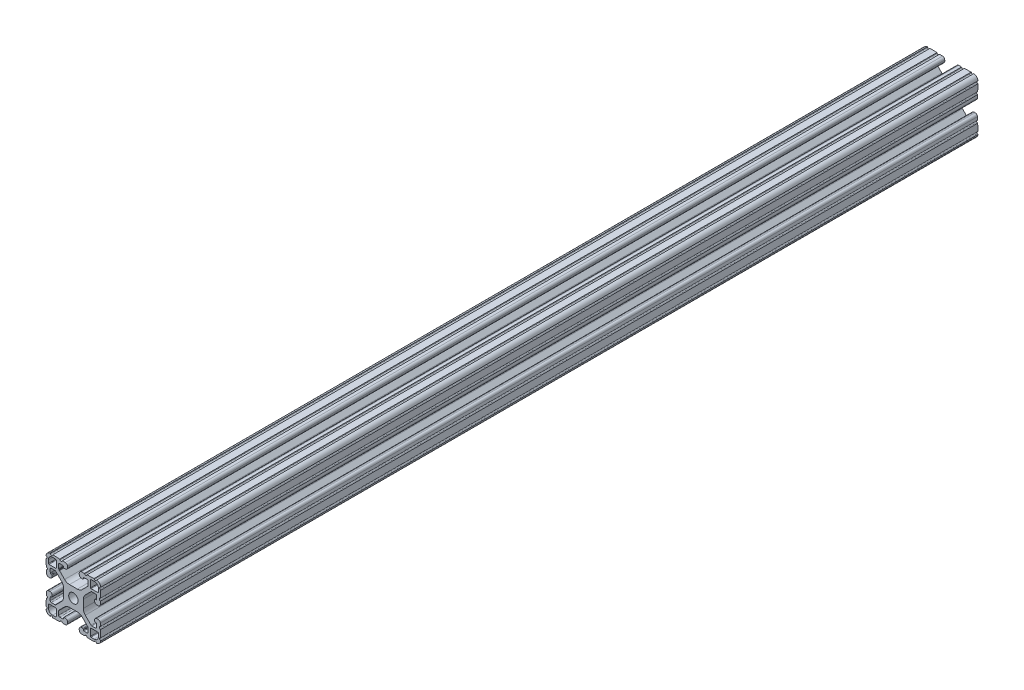
SolidWorks part; units mm, degrees
ref_plane "Front Plane" through (0, 0, 0) normal (0, 0, 1) x (1, 0, 0)
ref_plane "Top Plane" through (0, 0, 0) normal (0, 1, 0) x (1, 0, 0)
ref_plane "Right Plane" through (0, 0, 0) normal (1, 0, 0) x (0, 0, -1)
sketch "Sketch2" plane through (0, 0, 0) normal (0, 0, 1) x (1, 0, 0)
  line L0 (0, 19.05) -> (0, -19.05) construction
  line L1 (-19.05, 0) -> (19.05, 0) construction
  line L2 (4.064, -19.05) -> (19.05, -19.05) construction
  line L3 (19.05, -19.05) -> (19.05, -4.064) construction
  line L4 (4.064, -19.05) -> (4.064, -15.8768) construction
  line L5 (4.064, -15.8768) -> (13.7215, -15.8768) construction
  line L6 (13.7215, -15.8768) -> (4.7027, -6.858) construction
  line L7 (0, 0) -> (19.05, -19.05) construction
  line L8 (19.05, -4.064) -> (15.8768, -4.064) construction
  line L9 (15.8768, -4.064) -> (15.8768, -13.7215) construction
  line L10 (15.8768, -13.7215) -> (6.858, -4.7027) construction
  line L11 (11.3674, -9.2121) -> (9.2121, -11.3674) construction
  line L12 (10.287, -12.4423) -> (10.287, -15.8768) construction
  line L13 (15.7642, -19.0481) -> (4.064, -18.6395) construction
  line L14 (4.064, -18.6395) -> (4.2014, -14.7049) construction
  line L15 (4.2014, -14.7049) -> (6.858, -14.7977) construction
  line L16 (6.858, -14.7977) -> (6.858, -15.8768) construction
  line L17 (19.05, 4.064) -> (19.05, -4.064) construction
  line L18 (-19.05, -19.05) -> (19.05, -19.05) construction
  line L19 (-19.05, -19.05) -> (-19.05, 19.05) construction
  line L20 (-19.05, 19.05) -> (19.05, 19.05) construction
  line L21 (19.05, -19.05) -> (19.05, 19.05) construction
  line L22 (8.5725, -18.7969) -> (8.6004, -17.9973) construction
  line L23 (15.24, -19.0298) -> (15.2679, -18.2301) construction
  circle A0 centre (0, 0) radius 3.2639 construction
  arc A1 (18.1201, -18.1201) -> (15.7642, -19.0481) centre (15.875, -15.875) cw construction
  point P8 (0, -6.858)
  point P16 (10.2898, -10.2898)
  point P28 (11.8872, -11.8872)
  point P34 (8.5725, -18.7969)
  point P36 (15.24, -19.0298)
  point P38 (19.05, 0)
  dimension "D7" = 1.6002
  dimension "Center Hole Diameter" = 6.5278
  dimension "Corner Radius" = 3.175
  dimension "Slot Depth" = 12.192
  dimension "D1" = 3.048
  dimension "D3" = 2
  dimension "Flange Thickness" = 3.937
  dimension "D4" = 3.1732
  dimension "D2" = 20.574
  dimension "D5" = 13.716
  dimension "D6" = 7.1628
  dimension "D8" = 15.24
  dimension "D9" = 8.5725
  dimension "D10" = 0.8001
  dimension "Rail Height" = 38.1
  dimension "Rail Width" = 38.1
  dimension "T Slot Width" = 8.128
sketch "Sketch3" plane through (0, 0, 0) normal (1, 0, 0) x (0, 0, -1)
  line L0 (-304.8, 19.05) -> (304.8, 19.05) construction
  line L1 (-254, 0) -> (254, 0) construction
  dimension "Length" = 609.6
  dimension "D1" = 50.8
sketch "Sketch4" plane through (0, 0, 0) normal (0, 0, 1) x (1, 0, 0)
  line L1 (6.858, -14.7977) -> (6.858, -15.8768) construction
  line L2 (11.8872, -12.2682) -> (11.8872, -16.9436)
  line L3 (12.2549, -17.3243) -> (14.4454, -17.4008)
  line L7 (12.2682, -11.8872) -> (16.9436, -11.8872)
  line L9 (17.3243, -12.2549) -> (17.4008, -14.4454)
  line L22 (0, 0) -> (19.05, -19.05) construction
  line L23 (15.7642, -19.0481) -> (5.5961, -18.693)
  line L24 (4.064, -17.1065) -> (4.064, -16.344)
  line L25 (5.7069, -14.7575) -> (6.4903, -14.7848)
  line L26 (6.858, -15.1656) -> (6.858, -15.6891)
  line L27 (7.2257, -16.0699) -> (9.4655, -16.1481)
  line L28 (10.287, -15.3549) -> (10.287, -12.771)
  line L29 (10.0545, -12.2098) -> (6.0939, -8.2492)
  line L30 (2.7353, -6.858) -> (0, -6.858)
  line L31 (13.7215, -15.8768) -> (4.7027, -6.858) construction
  line L32 (4.064, -19.05) -> (19.05, -19.05) construction
  line L33 (4.064, -19.05) -> (4.064, -15.8768) construction
  line L34 (0, 19.05) -> (0, -19.05) construction
  line L35 (0, -3.2639) -> (0, -6.858)
  line L36 (0, 0) -> (19.1669, -19.1669) construction
  line L46 (10.287, -12.4423) -> (10.287, -15.8768) construction
  line L47 (6.858, -2.7353) -> (6.858, 0)
  line L48 (12.2098, -10.0545) -> (8.2492, -6.0939)
  line L49 (15.3549, -10.287) -> (12.771, -10.287)
  line L50 (16.0699, -7.2257) -> (16.1481, -9.4655)
  line L51 (15.1656, -6.858) -> (15.6891, -6.858)
  line L52 (14.7575, -5.7069) -> (14.7848, -6.4903)
  line L53 (17.1065, -4.064) -> (16.344, -4.064)
  line L54 (19.0481, -15.7642) -> (18.693, -5.5961)
  line L55 (3.2639, 0) -> (6.858, 0)
  arc A1 (14.4454, -17.4008) -> (17.4008, -14.4454) centre (14.5451, -14.5451) ccw
  arc A10 (16.9436, -11.8872) -> (17.3243, -12.2549) centre (16.9436, -12.2682) cw
  arc A12 (19.0481, -15.7642) -> (15.7642, -19.0481) centre (15.875, -15.875) cw
  arc A13 (3.2639, 0) -> (0, -3.2639) centre (0, 0) cw
  circle A14 centre (0, 0) radius 3.2639 construction
  arc A16 (6.0939, -8.2492) -> (2.7353, -6.858) centre (2.7353, -11.6078) ccw
  arc A17 (5.5961, -18.693) -> (4.064, -17.1065) centre (5.6515, -17.1065) cw
  arc A18 (4.064, -16.344) -> (5.7069, -14.7575) centre (5.6515, -16.344) cw
  arc A19 (9.4655, -16.1481) -> (10.287, -15.3549) centre (9.4933, -15.3549) ccw
  arc A20 (10.287, -12.771) -> (10.0545, -12.2098) centre (9.4933, -12.771) ccw
  arc A21 (6.4903, -14.7848) -> (6.858, -15.1656) centre (6.477, -15.1656) cw
  arc A22 (6.858, -15.6891) -> (7.2257, -16.0699) centre (7.239, -15.6891) ccw
  arc A23 (15.6891, -6.858) -> (16.0699, -7.2257) centre (15.6891, -7.239) cw
  arc A24 (14.7848, -6.4903) -> (15.1656, -6.858) centre (15.1656, -6.477) ccw
  arc A25 (12.771, -10.287) -> (12.2098, -10.0545) centre (12.771, -9.4933) cw
  arc A26 (16.1481, -9.4655) -> (15.3549, -10.287) centre (15.3549, -9.4933) cw
  arc A27 (16.344, -4.064) -> (14.7575, -5.7069) centre (16.344, -5.6515) ccw
  arc A28 (18.693, -5.5961) -> (17.1065, -4.064) centre (17.1065, -5.6515) ccw
  arc A29 (8.2492, -6.0939) -> (6.858, -2.7353) centre (11.6078, -2.7353) cw
  arc A30 (15.7642, -19.0481) -> (18.1201, -18.1201) centre (15.875, -15.875) ccw construction
  arc A31 (11.8872, -12.2682) -> (12.2682, -11.8872) centre (12.2682, -12.2682) cw
  arc A32 (11.8872, -16.9436) -> (12.2549, -17.3243) centre (12.2682, -16.9436) ccw
  point P33 (4.064, -18.6395)
  point P42 (6.858, -4.7027)
  point P45 (4.7027, -6.858)
  point P76 (18.6395, -4.064)
  point P89 (11.8872, -11.8872)
  dimension "D2" = 4.7498
  dimension "D3" = 0.7937
  dimension "D5" = 0.381
  dimension "D6" = 1.5875
  dimension "D8" = 2.8575
  dimension "D1" = 2
  dimension "D4" = 2.6784
  dimension "D7" = 1.6002
extrude "Boss-Extrude1" add sketch "Sketch4" along normal mid plane 609.6
sketch "Sketch8" plane through (0, 0, 0) normal (0, 0, 1) x (1, 0, 0)
  line L0 (7.6492, -18.7647) -> (9.4958, -18.8292)
  line L1 (15.7642, -19.0481) -> (4.064, -18.6395) construction
  line L2 (9.4958, -18.8292) -> (9.2789, -18.4213)
  line L3 (7.894, -18.3729) -> (7.6492, -18.7647)
  line L4 (8.5725, -18.7969) -> (8.6004, -17.9973) construction
  line L5 (14.3167, -18.9975) -> (16.1633, -19.062)
  line L7 (16.1633, -19.062) -> (15.9464, -18.6541)
  line L8 (14.5615, -18.6058) -> (14.3167, -18.9975)
  line L9 (15.24, -19.0298) -> (15.2679, -18.2301) construction
  line L10 (0, 0) -> (19.05, -19.05) construction
  line L11 (18.6058, -14.5615) -> (18.9975, -14.3167)
  line L12 (19.062, -16.1633) -> (18.6541, -15.9464)
  line L13 (18.9975, -14.3167) -> (19.062, -16.1633)
  line L14 (18.3729, -7.894) -> (18.7647, -7.6492)
  line L15 (18.8292, -9.4958) -> (18.4213, -9.2789)
  line L16 (18.7647, -7.6492) -> (18.8292, -9.4958)
  arc A0 (9.2789, -18.4213) -> (7.894, -18.3729) centre (8.5725, -18.7969) ccw
  arc A1 (15.9464, -18.6541) -> (14.5615, -18.6058) centre (15.24, -19.0298) ccw
  arc A2 (18.6541, -15.9464) -> (18.6058, -14.5615) centre (19.0298, -15.24) cw
  arc A3 (18.4213, -9.2789) -> (18.3729, -7.894) centre (18.7969, -8.5725) cw
  dimension "D1" = 60
extrude "Cut-Extrude2" cut sketch "Sketch8" against normal through all both and the other way through all
mirror "Mirror1" about plane through (0, 0, 0) normal (1, 0, 0) of bodies 142 134
mirror "Mirror2" about plane through (0, 0, 0) normal (0, 1, 0) of bodies 135
sketch "Sketch5" plane through (0, 0, 0) normal (0, 0, 1) x (1, 0, 0)
  line L0 (-6.0939, 8.2492) -> (-10.0545, 12.2098) construction
  line L1 (-10.1338, 12.508) -> (-10.1338, 12)
  line L2 (-9.9645, 11.8306) -> (-9.6506, 11.8306)
  line L3 (-9.6506, 11.8306) -> (-9.6506, 12.508)
  line L4 (-9.6506, 12.508) -> (-10.1338, 12.508)
  line L5 (-9.9046, 12.0598) -> (-9.9645, 12) construction
  circle A0 centre (-9.9046, 12.0598) radius 0.254 construction
  arc A1 (-10.287, 12.771) -> (-10.0545, 12.2098) centre (-9.4933, 12.771) ccw construction
  arc A2 (-10.1338, 12) -> (-9.9645, 11.8306) centre (-9.9645, 12) ccw
  dimension "D2" = 0.508
  dimension "D3" = 0.1693
  dimension "D1" = 0.7112
  dimension "D4" = 0.508
extrude "Cut-Extrude1" cut sketch "Sketch5" against normal through all both and the other way through all
ref_plane "Plane1" through (0, 19.05, 0) normal (0, 1, 0) x (-1, 0, 0)
ref_plane "Plane2" through (19.05, 0, 0) normal (1, 0, 0) x (0, 0, -1)
ref_plane "Plane3" through (0, -19.05, 0) normal (0, -1, 0) x (1, 0, 0)
ref_plane "Plane4" through (-19.05, 0, 0) normal (-1, 0, 0) x (0, 0, 1)
equation "\"D1@Boss-Extrude1\"=\"Length@Sketch3\""
equation "\"D6@Sketch4\"=\"Corner Radius@Sketch2\"/2"
equation "\"D3@Sketch4\"=\"D6@Sketch4\"/2"
equation "\"D4@Sketch2\"=\"Flange Thickness@Sketch2\"*.806"
equation "\"D7@Sketch4\"=\"D7@Sketch2\""
equation "\"D8@Sketch4\"=\"Corner Radius@Sketch2\"*.9"
equation "\"D3@Sketch5\"=\"D2@Sketch5\"/3"
equation "\"D4@Sketch5\"=\"D2@Sketch5\""
equation "\"D8@Sketch2\"=\"Rail Width@Sketch2\"*.4"
equation "\"D9@Sketch2\"=\"Rail Width@Sketch2\"*.225"
equation "\"D10@Sketch2\"=\"D7@Sketch2\"/2"
